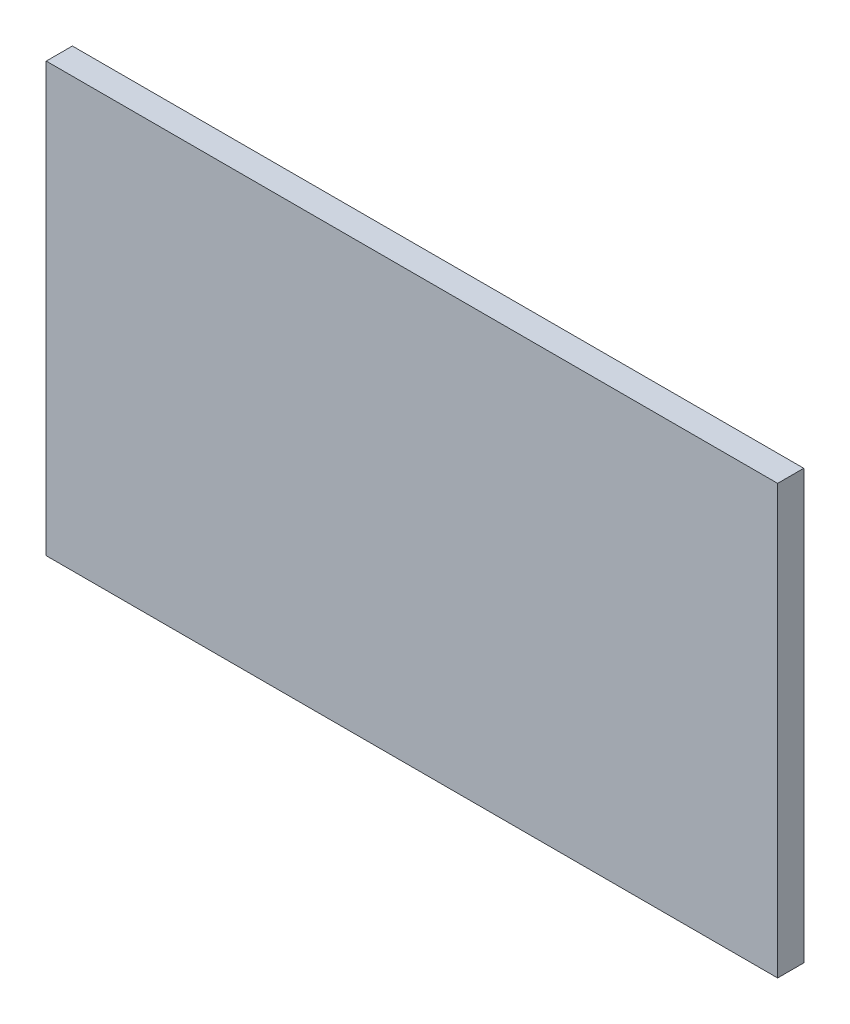
SolidWorks part; units mm, degrees
ref_plane "Front Plane" through (0, 0, 0) normal (0, 0, 1) x (1, 0, 0)
ref_plane "Top Plane" through (0, 0, 0) normal (0, 1, 0) x (1, 0, 0)
ref_plane "Right Plane" through (0, 0, 0) normal (1, 0, 0) x (0, 0, -1)
sketch "Sketch1" plane through (0, 0, 0) normal (0, 0, 1) x (1, 0, 0)
  line L1 (0, 0) -> (88.9, 0)
  line L2 (0, 0) -> (0, 52.07)
  line L3 (0, 52.07) -> (88.9, 52.07)
  line L4 (88.9, 0) -> (88.9, 52.07)
  dimension "D1" = 88.9
  dimension "D2" = 52.07
extrude "Boss-Extrude1" add sketch "Sketch1" along normal blind 3.175
